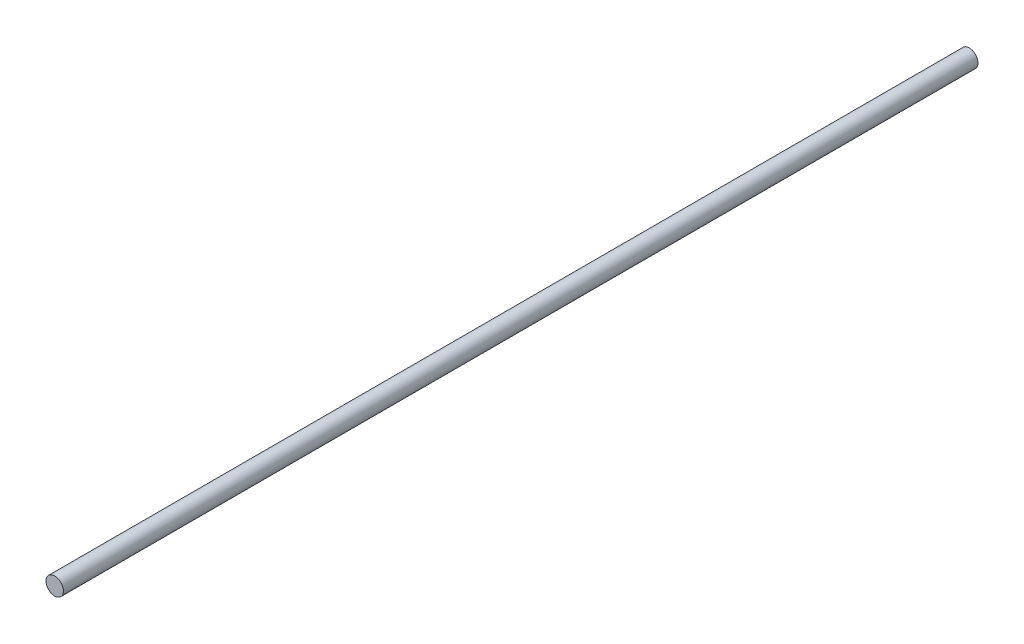
SolidWorks part; units mm, degrees
ref_plane "Plan de face" through (0, 0, 0) normal (0, 0, 1) x (1, 0, 0)
ref_plane "Plan de dessus" through (0, 0, 0) normal (0, 1, 0) x (1, 0, 0)
ref_plane "Plan de droite" through (0, 0, 0) normal (1, 0, 0) x (0, 0, -1)
sketch "Esquisse1" plane through (0, 0, 0) normal (0, 0, 1) x (1, 0, 0)
  circle A0 centre (0, 0) radius 4
  dimension "D1" = 8
extrude "Boss.-Extru.1" add sketch "Esquisse1" along normal blind 420
